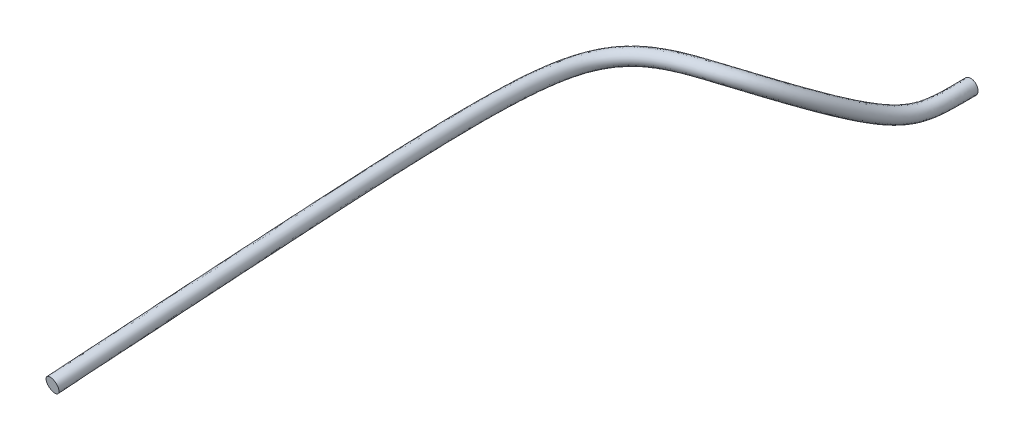
SolidWorks part; units mm, degrees
ref_plane "Front" through (0, 0, 0) normal (0, 0, 1) x (1, 0, 0)
ref_plane "Top" through (0, 0, 0) normal (0, 1, 0) x (1, 0, 0)
ref_plane "Right" through (0, 0, 0) normal (1, 0, 0) x (0, 0, -1)
sketch "Sketch1" plane through (0, 0, 0) normal (0, 0, 1) x (1, 0, 0)
  line L0 (0, 1.15) -> (0, -1.15) construction
  line L2 (1.15, 0) -> (0, 0) construction
  circle A0 centre (0, 0) radius 1.15
  dimension "D1" = 2.3
sketch3d "3DSketch1"
  line L1 (0, 0, 0) -> (0, 0, 5.3857) construction
  line L2 (0, 1.15, 0) -> (0, -1.15, 0) construction
  line L3 (1.15, 0, 0) -> (0, 0, 0) construction
  spline S0 degree 3 poles (0, 0, 0) (0, 0, 5.5543) (-0.9257, -1.4755, 10.0256) (-7.9682, 12.9946, 30.6683) (-32.6951, 5.2549, 29.034) (-25.7181, 10.0675, 61.1851) (-31.9989, -0.1151, 113.9015) knots 0 0 0 0 0.255985 0.525952 0.698297 1 1 1 1
  point P8 (0.4739, 7.5416, 20.5164)
  point P13 (0, 0, 0)
  point P14 (-1.448, 1.9724, 13.3046)
  point P15 (-1.9106, 2.1211, 13.2033)
  point P16 (-1.7852, 2.3999, 13.5764)
  point P17 (-1.8056, 1.7464, 12.9613)
  point P18 (-1.9569, 1.8298, 12.9242)
  point P19 (0, 0, 0)
  point P20 (-2.9315, 16.6918, 38.6479)
  point P21 (-10.6146, 15.2678, 42.0455)
  point P22 (-26.4681, 3.2433, 65.2741)
  point P23 (-1.0354, 1.5502, 127.6737)
  point P24 (-28.0135, 8.5642, 82.8155)
  point P25 (-13.2772, 19.7036, 34.2107)
  point P26 (-27.803, 16.0569, 45.4909)
  point P27 (-32.0889, 13.842, 73.0865)
  point P28 (-31.6589, 4.2914, 114.6284)
  point P29 (0, 0, 0)
  point P30 (0, 0, 0)
  point P31 (-25.1904, 11.4927, 72.1204)
sweep "Sweep1" add profiles "Sketch1" path "3DSketch1"
